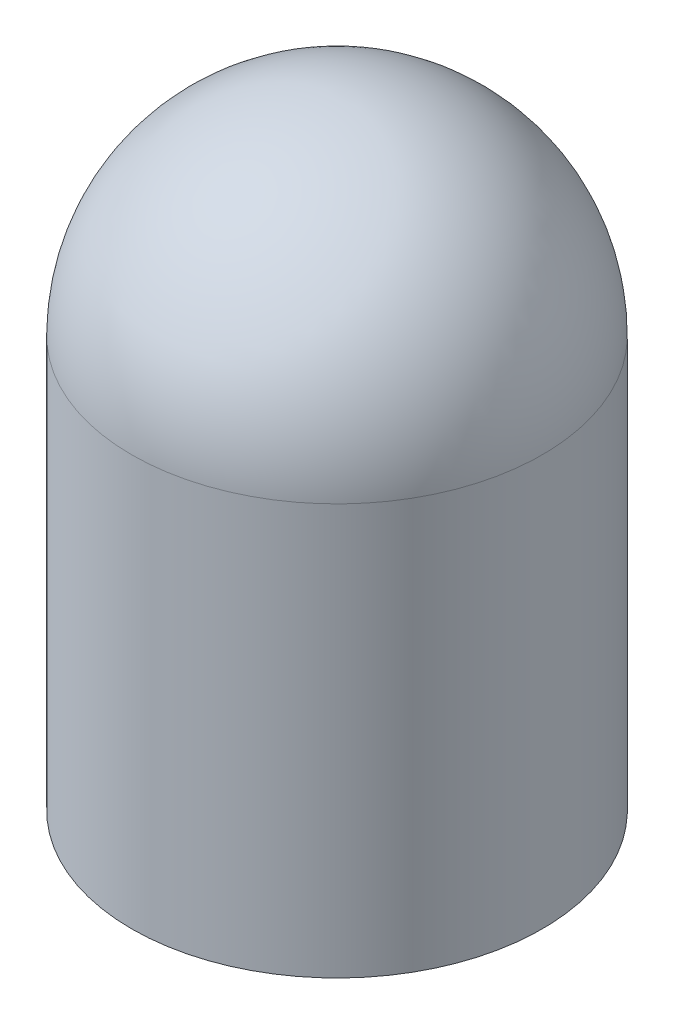
SolidWorks part; units mm, degrees
ref_plane "Front Plane" through (0, 0, 0) normal (0, 0, 1) x (1, 0, 0)
ref_plane "Top Plane" through (0, 0, 0) normal (0, 1, 0) x (1, 0, 0)
ref_plane "Right Plane" through (0, 0, 0) normal (1, 0, 0) x (0, 0, -1)
sketch "Sketch1" plane through (0, 0, 0) normal (0, 1, 0) x (1, 0, 0)
  circle A0 centre (0, 0) radius 3.175
  dimension "D1" = 6.35
extrude "Extrude1" add sketch "Sketch1" along normal blind 9.525
fillet "Fillet1" radius 3.175 1 edges at (0, 9.525, 3.175)
